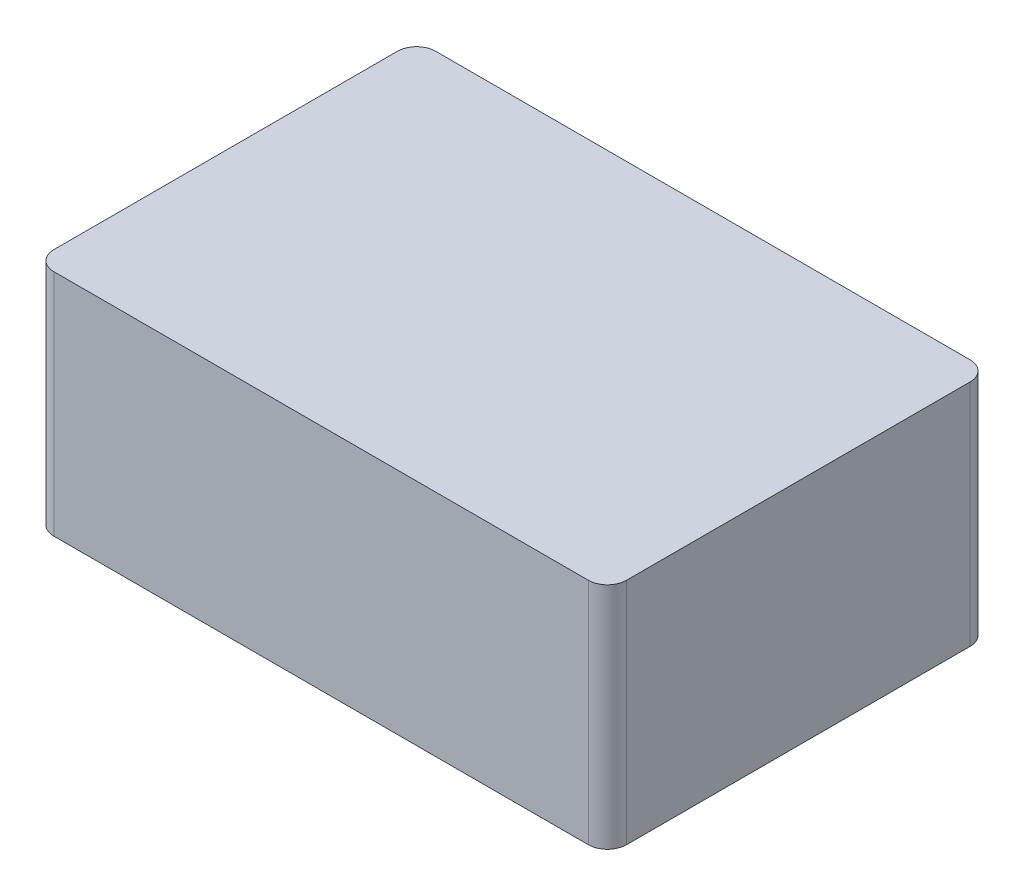
SolidWorks part; units mm, degrees
ref_plane "Front Plane" through (0, 0, 0) normal (0, 0, 1) x (1, 0, 0)
ref_plane "Top Plane" through (0, 0, 0) normal (0, 1, 0) x (1, 0, 0)
ref_plane "Right Plane" through (0, 0, 0) normal (1, 0, 0) x (0, 0, -1)
sketch "Sketch1" plane through (0, 0, 0) normal (0, 1, 0) x (1, 0, 0)
  line L1 (0, 0) -> (150, 0)
  line L2 (0, 0) -> (0, 100)
  line L3 (0, 100) -> (150, 100)
  line L4 (150, 0) -> (150, 100)
  dimension "D1" = 100
  dimension "D2" = 150
extrude "Boss-Extrude1" add sketch "Sketch1" along normal blind 60
shell "Shell1" thickness 3
sketch "Sketch2" plane through (0, 57, 0) normal (0, -1, 0) x (1, 0, 0)
  line L0 (147, -97) -> (3, -97) construction
  line L1 (18, -88) -> (22, -88)
  line L2 (18, -88) -> (18, -92)
  line L3 (18, -92) -> (22, -92)
  line L4 (22, -88) -> (22, -92)
  line L5 (3, -97) -> (3, -3) construction
  line L6 (3, -97) -> (3, -3) construction
  line L7 (62.26, -88) -> (66.26, -88)
  line L8 (62.26, -88) -> (62.26, -92)
  line L9 (62.26, -92) -> (66.26, -92)
  line L10 (66.26, -88) -> (66.26, -92)
  line L11 (18, -36.12) -> (22, -36.12)
  line L12 (18, -36.12) -> (18, -40.12)
  line L13 (18, -40.12) -> (22, -40.12)
  line L14 (22, -36.12) -> (22, -40.12)
  line L16 (62.26, -36.12) -> (66.26, -36.12)
  line L17 (62.26, -36.12) -> (62.26, -40.12)
  line L18 (62.26, -40.12) -> (66.26, -40.12)
  line L19 (66.26, -36.12) -> (66.26, -40.12)
  point P12 (66.26, -90)
  point P19 (18, -38.12)
  dimension "D1" = 4
  dimension "D2" = 4
  dimension "D3" = 5
  dimension "D4" = 15
  dimension "D5" = 4
  dimension "D6" = 4
  dimension "D7" = 48.26
  dimension "D8" = 5
  dimension "D9" = 4
  dimension "D10" = 4
  dimension "D11" = 55.88
  dimension "D12" = 15
  dimension "D13" = 4
  dimension "D14" = 4
  dimension "D15" = 48.26
  dimension "D16" = 55.88
extrude "Boss-Extrude2" add sketch "Sketch2" along normal blind 20
sketch "Sketch3" plane through (0, 37, 0) normal (0, -1, 0) x (1, 0, 0)
  line L0 (18, -92) -> (22, -92) construction
  line L1 (18, -88) -> (18, -92) construction
  line L2 (18, -36.12) -> (18, -40.12) construction
  line L3 (22, -36.12) -> (18, -36.12) construction
  line L4 (66.26, -36.12) -> (62.26, -36.12) construction
  line L6 (66.26, -40.12) -> (66.26, -36.12) construction
  line L7 (66.26, -92) -> (66.26, -88) construction
  line L8 (62.26, -92) -> (66.26, -92) construction
  circle A0 centre (20.3, -89.7) radius 0.85
  circle A1 centre (20.3, -38.42) radius 0.85
  circle A2 centre (63.96, -38.42) radius 0.85
  circle A3 centre (63.96, -89.7) radius 0.85
  dimension "D1" = 2.3
  dimension "D3" = 2.3
  dimension "D5" = 2.3
  dimension "D7" = 2.3
  dimension "D2" = 2.3
  dimension "D4" = 2.3
  dimension "D6" = 2.3
  dimension "D8" = 2.3
extrude "Cut-Extrude1" cut sketch "Sketch3" against normal blind 10
sketch "Sketch4" plane through (0, 57, 0) normal (0, -1, 0) x (1, 0, 0)
  line L0 (3, -3) -> (147, -3) construction
  line L1 (20, -6) -> (71, -6)
  line L2 (20, -6) -> (20, -34.5)
  line L3 (20, -34.5) -> (71, -34.5)
  line L4 (71, -6) -> (71, -34.5)
  line L5 (3, -97) -> (3, -3) construction
  dimension "D1" = 51
  dimension "D2" = 28.5
  dimension "D3" = 3
  dimension "D4" = 17
extrude "Boss-Extrude3" add sketch "Sketch4" along normal blind 57
sketch "Sketch5" plane through (0, 0, 0) normal (0, -1, 0) x (1, 0, 0)
  line L0 (71, -6) -> (20, -6) construction
  line L1 (21, -7) -> (70, -7)
  line L2 (21, -7) -> (21, -33.5)
  line L3 (21, -33.5) -> (70, -33.5)
  line L4 (70, -7) -> (70, -33.5)
  line L5 (20, -34.5) -> (71, -34.5) construction
  line L6 (20, -6) -> (20, -34.5) construction
  line L7 (71, -34.5) -> (71, -6) construction
  dimension "D1" = 1
  dimension "D2" = 1
  dimension "D3" = 1
  dimension "D4" = 1
extrude "Cut-Extrude2" cut sketch "Sketch5" against normal blind 17.5
sketch "Sketch6" plane through (71, 0, 0) normal (1, 0, 0) x (0, 0, -1)
  line L0 (34.5, 0) -> (6, 0) construction
  line L1 (24.2883, 0) -> (31.6043, 0)
  line L2 (24.2883, 0) -> (24.2883, 10.0635)
  line L3 (24.2883, 10.0635) -> (31.6043, 10.0635)
  line L4 (31.6043, 0) -> (31.6043, 10.0635)
  line L5 (18.2511, 0) -> (8.2595, 0)
  line L6 (18.2511, 0) -> (18.2511, 9.8768)
  line L7 (18.2511, 9.8768) -> (8.2595, 9.8768)
  line L8 (8.2595, 0) -> (8.2595, 9.8768)
extrude "Cut-Extrude3" cut sketch "Sketch6" against normal blind 1
ref_plane "Plane1" through (0, 47, 0) normal (0, -1, 0) x (-1, 0, 0)
sketch "Sketch7" plane through (0, 47, 0) normal (0, -1, 0) x (-1, 0, 0)
  line L0 (-13.0246, 80.6919) -> (-135.6442, 80.6919)
  line L1 (-75.4437, 87.9396) -> (-75.4437, 15.0186)
  line L2 (-118.3384, 86.9042) -> (-118.3384, 15.0186)
  line L3 (-35.2115, 92.0812) -> (-35.2115, 37.9451)
  line L4 (-135.6442, 57.1738) -> (-11.3975, 57.1738)
rib "Rib1" sketch "Sketch7" sketch "Sketch7" thickness 2 extrusion direction normal to sketch draft on no parameters "D1"=2
sketch "Sketch8" plane through (0, 57, 0) normal (0, -1, 0) x (1, 0, 0)
  line L1 (3, -3) -> (10, -3)
  line L2 (3, -3) -> (3, -10)
  line L3 (3, -10) -> (10, -10)
  line L4 (10, -3) -> (10, -10)
  point P4 (6.5, -10)
  dimension "D1" = 7
  dimension "D2" = 7
extrude "Boss-Extrude4" add sketch "Sketch8" along normal blind 57
ref_plane "Plane2" through (0, 0, -50) normal (0, 0, 1) x (1, 0, 0)
mirror "Mirror1" about plane through (0, 0, -50) normal (0, 0, 1) of "Boss-Extrude4"
ref_plane "Plane3" through (75, 0, 0) normal (-1, 0, 0) x (0, 0, 1)
mirror "Mirror2" about plane through (75, 0, 0) normal (-1, 0, 0) of "Mirror1", "Boss-Extrude4"
sketch "Sketch9" plane through (0, 0, 0) normal (0, -1, 0) x (1, 0, 0)
  line L0 (0, -100) -> (0, 0) construction
  line L1 (0, 0) -> (150, 0) construction
  circle A0 centre (5, -5) radius 2
  dimension "D1" = 5
  dimension "D2" = 5
extrude "Cut-Extrude4" cut sketch "Sketch9" against normal blind 10
mirror "Mirror3" about plane through (0, 0, -50) normal (0, 0, 1) of "Cut-Extrude4"
mirror "Mirror4" about plane through (75, 0, 0) normal (-1, 0, 0) of "Mirror3", "Cut-Extrude4"
fillet "Fillet1" radius 5 4 edges at (0, 30, -100) (150, 30, -100) (150, 30, 0) (0, 30, 0)
